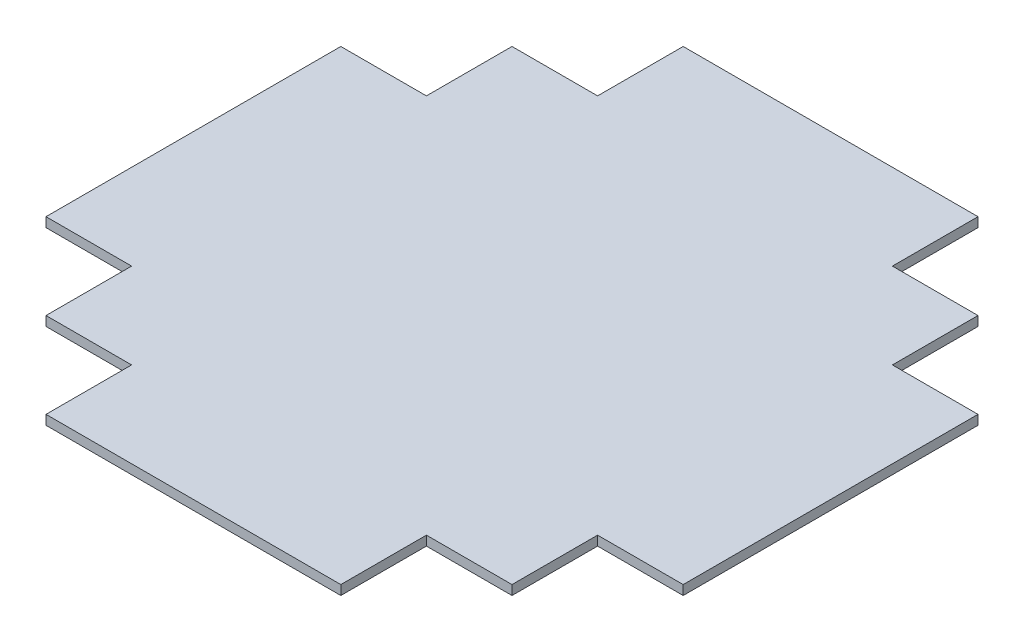
SolidWorks part; units mm, degrees
ref_plane "Front Plane" through (0, 0, 0) normal (0, 0, 1) x (1, 0, 0)
ref_plane "Top Plane" through (0, 0, 0) normal (0, 1, 0) x (1, 0, 0)
ref_plane "Right Plane" through (0, 0, 0) normal (1, 0, 0) x (0, 0, -1)
sketch "Sketch1" plane through (0, 0, 0) normal (0, 1, 0) x (1, 0, 0)
  line L1 (-62, 0) -> (-62, -18)
  line L2 (-62, -18) -> (-80, -18)
  line L12 (-80, -18) -> (-80, -36)
  line L13 (-80, -36) -> (-98, -36)
  line L14 (-98, -36) -> (-98, -98)
  line L15 (-98, -98) -> (-80, -98)
  line L16 (-80, -98) -> (-80, -116)
  line L17 (-80, -116) -> (-62, -116)
  line L19 (-62, -134) -> (0, -134)
  line L21 (0, -116) -> (18, -116)
  line L22 (18, -116) -> (18, -98)
  line L23 (18, -98) -> (36, -98)
  line L24 (36, -98) -> (36, -36)
  line L26 (18, -36) -> (18, -18)
  line L27 (-62, 0) -> (0, 0)
  line L28 (0, 0) -> (0, -18)
  line L29 (-62, -116) -> (-62, -134)
  line L30 (0, -134) -> (0, -116)
  line L31 (0, -18) -> (18, -18)
  line L32 (18, -36) -> (36, -36)
  dimension "D1" = 62
  dimension "D2" = 62
  dimension "D3" = 62
  dimension "D4" = 18
  dimension "D5" = 18
  dimension "D6" = 18
  dimension "D7" = 18
  dimension "D8" = 18
  dimension "D9" = 18
  dimension "D10" = 134
  dimension "D11" = 18
  dimension "D12" = 18
  dimension "D13" = 18
  dimension "D14" = 18
  dimension "D15" = 18
  dimension "D16" = 18
  dimension "D17" = 18
  dimension "D18" = 18
extrude "Boss-Extrude1" add sketch "Sketch1" along normal blind 2
